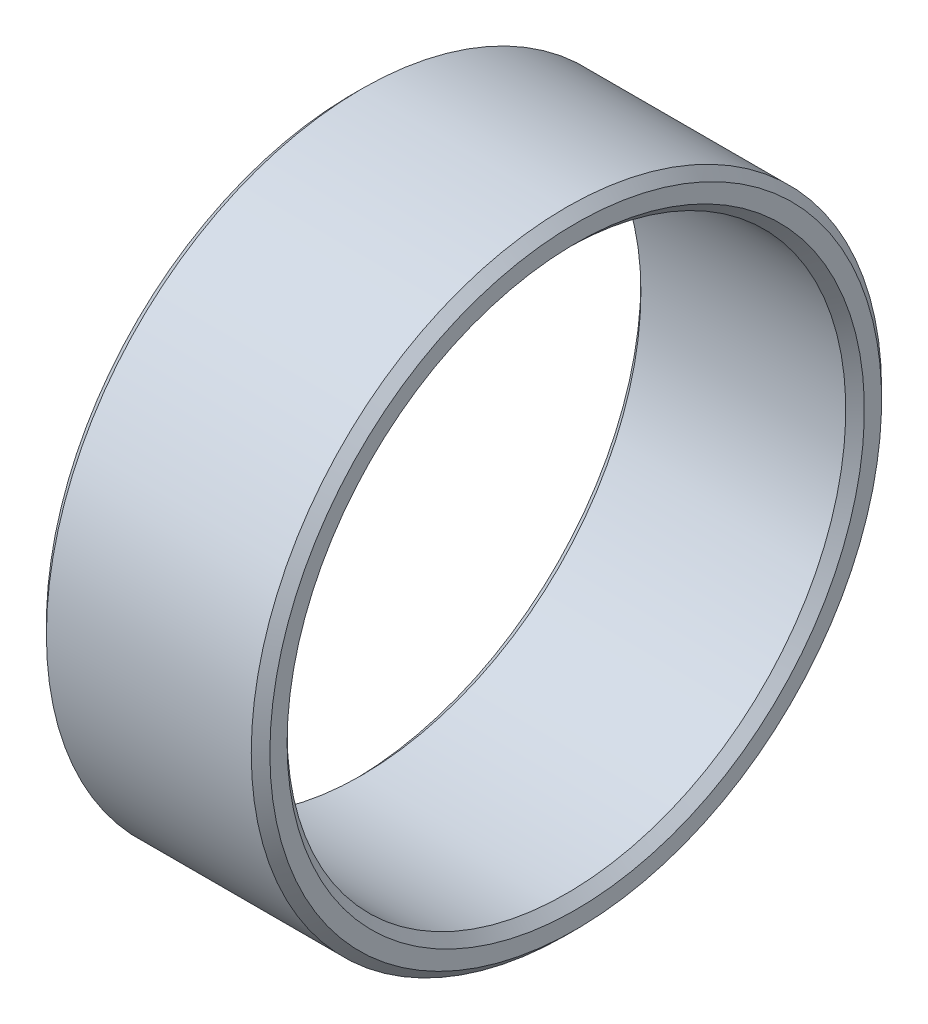
SolidWorks part; units mm, degrees
material "POM Acetal Copolymer"
ref_plane "Front Plane" through (0, 0, 0) normal (0, 0, 1) x (1, 0, 0)
ref_plane "Top Plane" through (0, 0, 0) normal (0, 1, 0) x (1, 0, 0)
ref_plane "Right Plane" through (0, 0, 0) normal (1, 0, 0) x (0, 0, -1)
sketch "Sketch1" plane through (0, 0, 0) normal (0, 0, 1) x (1, 0, 0)
  line L0 (0, 0) -> (0, 52.73) construction
  line L1 (-6, 16.925) -> (6, 16.925)
  line L2 (-6, 16.925) -> (-6, 15)
  line L3 (-6, 15) -> (6, 15)
  line L4 (6, 16.925) -> (6, 15)
  line L5 (0, 0) -> (10.5756, 0) construction
  dimension "D1" = 15
  dimension "D2" = 33.85
  dimension "D3" = 12
revolve "Revolve1" add sketch "Sketch1" angle 360 about L5
chamfer "Chamfer1" distance 0.5 angle 45 4 edges at (6, 0, 15) (6, 0, 16.925) (-6, 0, 15) (-6, 0, 16.925)
